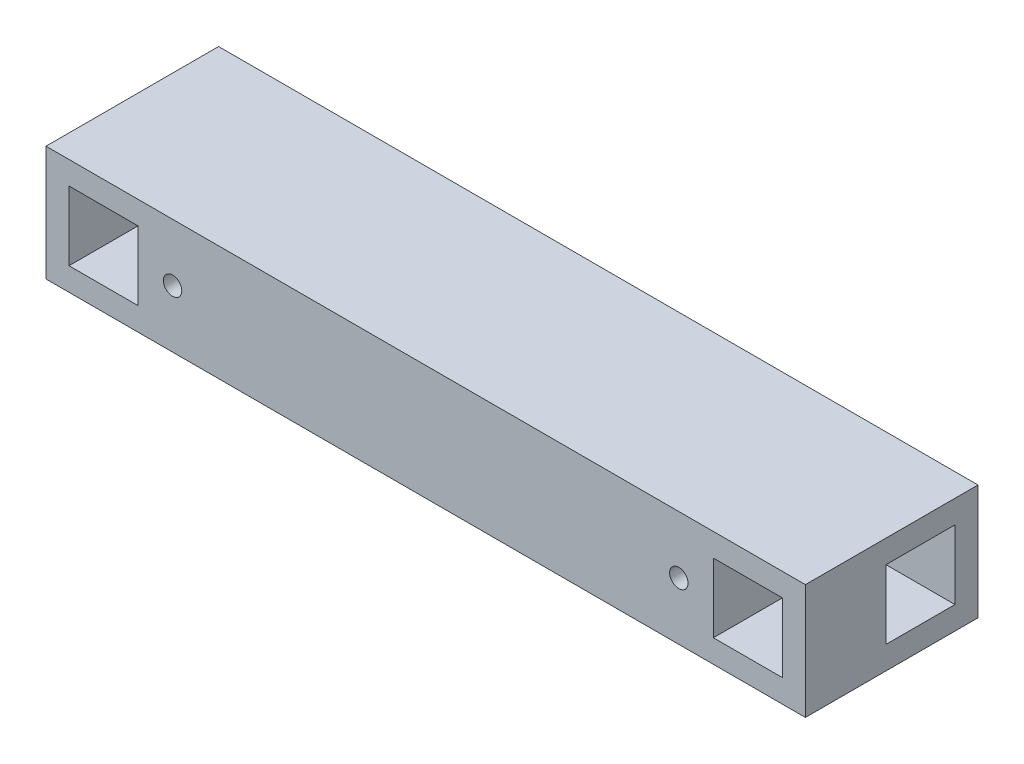
SolidWorks part; units mm, degrees
material "ABS"
ref_plane "Alzado" through (0, 0, 0) normal (0, 0, 1) x (1, 0, 0)
ref_plane "Planta" through (0, 0, 0) normal (0, 1, 0) x (1, 0, 0)
ref_plane "Vista lateral" through (0, 0, 0) normal (1, 0, 0) x (0, 0, -1)
sketch "Croquis1" plane through (0, 0, 0) normal (0, 0, 1) x (1, 0, 0)
  line L1 (-165, -25) -> (165, -25)
  line L2 (-165, -25) -> (-165, 25)
  line L3 (-165, 25) -> (165, 25)
  line L4 (165, -25) -> (165, 25)
  line L5 (-165, -25) -> (165, 25) construction
  line L6 (-165, 25) -> (165, -25) construction
  point P0 (0, 0)
  dimension "D1" = 50
  dimension "D2" = 330
extrude "Saliente-Extruir1" add sketch "Croquis1" along normal blind 75
sketch "Croquis2" plane through (0, 0, 75) normal (0, 0, 1) x (1, 0, 0)
  line L0 (0, 25) -> (0, -25) construction
  line L1 (-165, 25) -> (-155, 25) construction
  line L2 (-165, 25) -> (-165, 15) construction
  line L3 (-165, 15) -> (-155, 15) construction
  line L4 (-155, 25) -> (-155, 15) construction
  line L5 (-155, 15) -> (-125, 15)
  line L6 (-155, 15) -> (-155, -15)
  line L7 (-155, -15) -> (-125, -15)
  line L8 (-125, 15) -> (-125, -15)
  line L9 (165, 25) -> (-165, 25) construction
  line L10 (-165, -25) -> (165, -25) construction
  line L11 (155, 25) -> (155, 15) construction
  line L12 (165, 15) -> (155, 15) construction
  line L13 (165, 25) -> (165, 15) construction
  line L14 (165, 25) -> (155, 25) construction
  line L15 (125, 15) -> (125, -15)
  line L16 (155, -15) -> (125, -15)
  line L17 (155, 15) -> (155, -15)
  line L18 (155, 15) -> (125, 15)
  line L19 (-125, 0) -> (-110, 0) construction
  circle A0 centre (-110, 0) radius 4
  circle A1 centre (110, 0) radius 4
  dimension "D6" = 8
  dimension "D1" = 10
  dimension "D2" = 10
  dimension "D3" = 30
  dimension "D4" = 30
  dimension "D5" = 15
extrude "Cortar-Extruir1" cut sketch "Croquis2" against normal blind 30
sketch "Croquis3" plane through (-165, 0, 0) normal (-1, 0, 0) x (0, 0, 1)
  line L1 (0, 25) -> (10, 25) construction
  line L2 (0, 25) -> (0, 15) construction
  line L3 (0, 15) -> (10, 15) construction
  line L4 (10, 25) -> (10, 15) construction
  line L5 (10, 15) -> (40, 15)
  line L6 (10, 15) -> (10, -15)
  line L7 (10, -15) -> (40, -15)
  line L8 (40, 15) -> (40, -15)
  dimension "D1" = 10
  dimension "D2" = 10
  dimension "D3" = 30
  dimension "D4" = 30
extrude "Cortar-Extruir2" cut sketch "Croquis3" against normal through all
